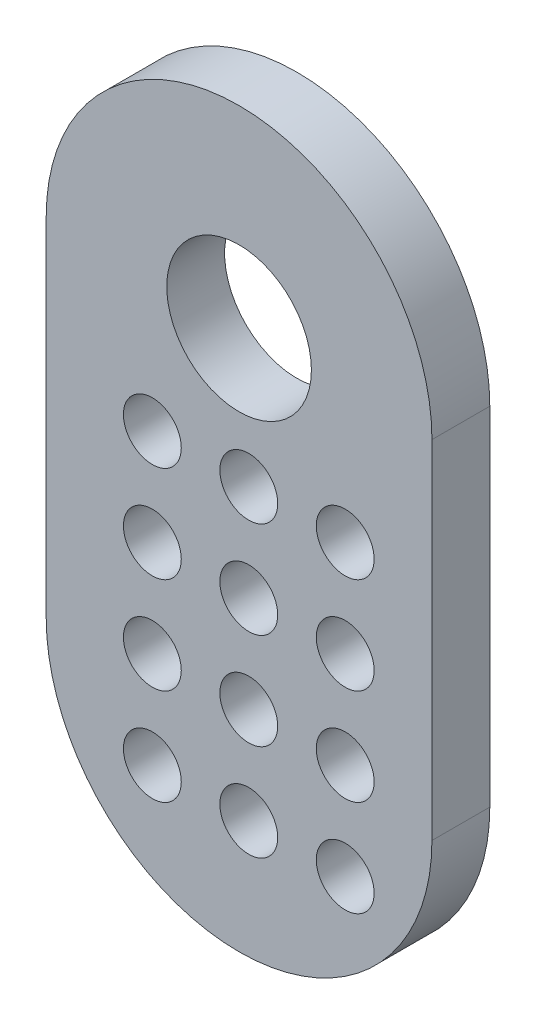
SolidWorks part; units mm, degrees
ref_plane "Plan de face" through (0, 0, 0) normal (0, 0, 1) x (1, 0, 0)
ref_plane "Plan de dessus" through (0, 0, 0) normal (0, 1, 0) x (1, 0, 0)
ref_plane "Plan de droite" through (0, 0, 0) normal (1, 0, 0) x (0, 0, -1)
sketch "Esquisse1" plane through (0, 0, 0) normal (0, 0, 1) x (1, 0, 0)
  line L9 (-10, 0) -> (-10, -18) construction
  line L10 (-10, -18) -> (10, -18) construction
  line L11 (10, -18) -> (10, 0) construction
  line L12 (-10, -18) -> (-10, 0)
  line L13 (10, -18) -> (10, 0)
  arc A2 (-10, 0) -> (10, 0) centre (0, 0) cw
  circle A3 centre (0, 0) radius 3.75
  circle A4 centre (-4.4966, -21.8672) radius 1.5
  circle A5 centre (0.5034, -21.8672) radius 1.5
  circle A6 centre (5.5034, -21.8672) radius 1.5
  circle A7 centre (0.5034, -16.8672) radius 1.5
  circle A8 centre (5.5034, -16.8672) radius 1.5
  circle A9 centre (0.5034, -11.8672) radius 1.5
  circle A10 centre (5.5034, -11.8672) radius 1.5
  circle A11 centre (0.5034, -6.8672) radius 1.5
  circle A12 centre (5.5034, -6.8672) radius 1.5
  circle A13 centre (-4.4966, -16.8672) radius 1.5
  circle A14 centre (-4.4966, -11.8672) radius 1.5
  circle A15 centre (-4.4966, -6.8672) radius 1.5
  arc A17 (-10, -18) -> (10, -18) centre (0, -18) ccw
  dimension "D6" = 3
  dimension "D2" = 7.5
  dimension "D3" = 10
  dimension "D4" = 18
  dimension "D1" = 0
  dimension "D9" = 3
  dimension "D10" = 4
extrude "Boss.-Extru.1" add sketch "Esquisse1" along normal blind 3 contours L12 A17 L13 A2 A3 A4 A5 A6 A7 A8 A9 A10 A11 A12 A13 A14 A15
